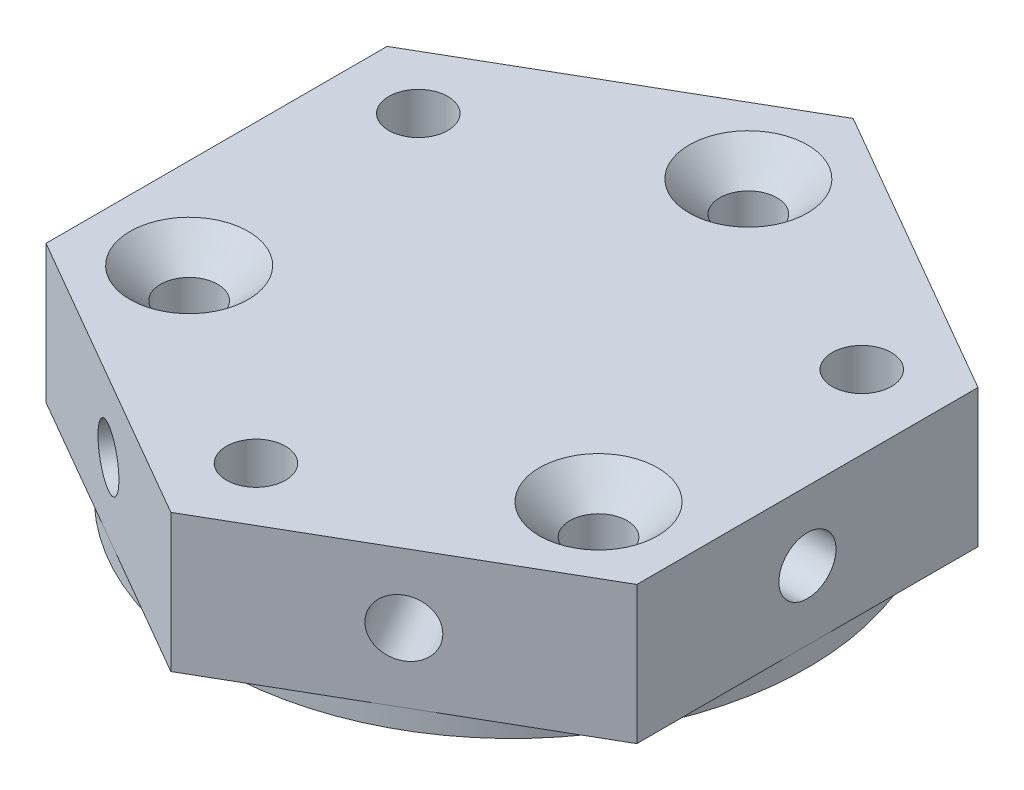
SolidWorks part; units mm, degrees
ref_plane "前视基准面" through (0, 0, 0) normal (0, 0, 1) x (1, 0, 0)
ref_plane "上视基准面" through (0, 0, 0) normal (0, 1, 0) x (1, 0, 0)
ref_plane "右视基准面" through (0, 0, 0) normal (1, 0, 0) x (0, 0, -1)
sketch "草图1" plane through (0, 0, 0) normal (0, 1, 0) x (1, 0, 0)
  line L0 (0, 0) -> (0, 33.3478) construction
  line L1 (0, 0) -> (11.2563, 0) construction
  line L2 (-10.3923, -6) -> (0, 0) construction
  line L3 (0, 0) -> (10.3923, -6) construction
  line L4 (0, 0) -> (-11.2583, 6.5) construction
  line L5 (11.2583, 6.5) -> (0, 0) construction
  circle A0 centre (0, 0) radius 15
  circle A1 centre (0, 12) radius 1.45
  circle A2 centre (0, 0) radius 12 construction
  circle A3 centre (-10.3923, -6) radius 1.45
  circle A4 centre (10.3923, -6) radius 1.45
  circle A5 centre (0, 0) radius 13 construction
  circle A6 centre (-11.2583, 6.5) radius 1.5
  circle A7 centre (0, -13) radius 1.5
  circle A8 centre (11.2583, 6.5) radius 1.5
  dimension "D1" = 30
  dimension "D2" = 24
  dimension "D3" = 2.9
  dimension "D6" = 26
  dimension "D8" = 3
  dimension "D4" = 120
  dimension "D5" = 120
  dimension "D7" = 60
  dimension "D9" = 60
extrude "凸台-拉伸1" add sketch "草图1" along normal blind 8
sketch "草图2" plane through (0, 8, 0) normal (0, 1, 0) x (1, 0, 0)
  line L0 (0, 17.3205) -> (0, 0) construction
  line L1 (0, 17.3205) -> (-15, 8.6603)
  line L2 (-15, 8.6603) -> (-15, -8.6603)
  line L3 (-15, -8.6603) -> (0, -17.3205)
  line L4 (0, -17.3205) -> (15, -8.6603)
  line L5 (15, -8.6603) -> (15, 8.6603)
  line L6 (15, 8.6603) -> (0, 17.3205)
  circle A0 centre (0, 0) radius 15 construction
  circle A1 centre (0, 12) radius 1.45
  circle A2 centre (0, 12) radius 1.45 construction
  circle A3 centre (-11.2583, 6.5) radius 1.5
  circle A4 centre (-11.2583, 6.5) radius 1.5 construction
  circle A5 centre (11.2583, 6.5) radius 1.5
  circle A6 centre (11.2583, 6.5) radius 1.5 construction
  circle A7 centre (-10.3923, -6) radius 1.45
  circle A8 centre (-10.3923, -6) radius 1.45 construction
  circle A9 centre (0, -13) radius 1.5
  circle A10 centre (0, -13) radius 1.5 construction
  circle A11 centre (10.3923, -6) radius 1.45
  circle A12 centre (10.3923, -6) radius 1.45 construction
  dimension "D1" = 30
extrude "凸台-拉伸2" add sketch "草图2" against normal blind 7
sketch "草图3" plane through (7.5, 0, 12.9904) normal (0.5, 0, 0.866) x (0.866, 0, -0.5)
  line L1 (0, 8) -> (0, 1) construction
  line L2 (-8.6603, 8) -> (8.6603, 8) construction
  circle A1 centre (0, 4.5) radius 1.45
  dimension "D1" = 2.9
extrude "切除-拉伸1" cut sketch "草图3" against normal blind 8
sketch "草图4" plane through (-7.5, 0, 12.9904) normal (-0.5, 0, 0.866) x (0.866, 0, 0.5)
  line L0 (0, 1) -> (0, 8) construction
  line L1 (-8.6603, 8) -> (8.6603, 8) construction
  circle A0 centre (0, 4.5) radius 1.45
  dimension "D1" = 2.9
extrude "切除-拉伸2" cut sketch "草图4" against normal blind 8
sketch "草图5" plane through (-15, 0, 0) normal (-1, 0, 0) x (0, 0, 1)
  line L0 (0, 1) -> (0, 8) construction
  line L1 (-8.6603, 8) -> (8.6603, 8) construction
  circle A0 centre (0, 4.5) radius 1.45
  dimension "D1" = 2.9
extrude "切除-拉伸3" cut sketch "草图5" against normal blind 8
sketch "草图6" plane through (15, 0, 0) normal (1, 0, 0) x (0, 0, -1)
  line L0 (0, 8) -> (0, 1) construction
  line L1 (-8.6603, 8) -> (8.6603, 8) construction
  circle A0 centre (0, 4.5) radius 1.45
  dimension "D1" = 2.9
extrude "切除-拉伸4" cut sketch "草图6" against normal blind 8
sketch "草图7" plane through (7.5, 0, -12.9904) normal (0.5, 0, -0.866) x (-0.866, 0, -0.5)
  line L0 (0, 8) -> (0, 1) construction
  line L1 (-8.6603, 8) -> (8.6603, 8) construction
  circle A0 centre (0, 4.5) radius 1.45
  dimension "D1" = 2.9
extrude "切除-拉伸5" cut sketch "草图7" against normal blind 8
sketch "草图8" plane through (-7.5, 0, -12.9904) normal (-0.5, 0, -0.866) x (-0.866, 0, 0.5)
  line L0 (0, 8) -> (0, 4.5) construction
  line L1 (-8.6603, 8) -> (8.6603, 8) construction
  circle A0 centre (0, 4.5) radius 1.5
  dimension "D1" = 3
  dimension "D2" = 3.5
extrude "切除-拉伸6" cut sketch "草图8" against normal blind 8
chamfer "倒角1" distance 1.55 angle 45 3 edges at (-10.3923, 8, 7.45) (0, 8, -10.55) (10.3923, 8, 7.45)
